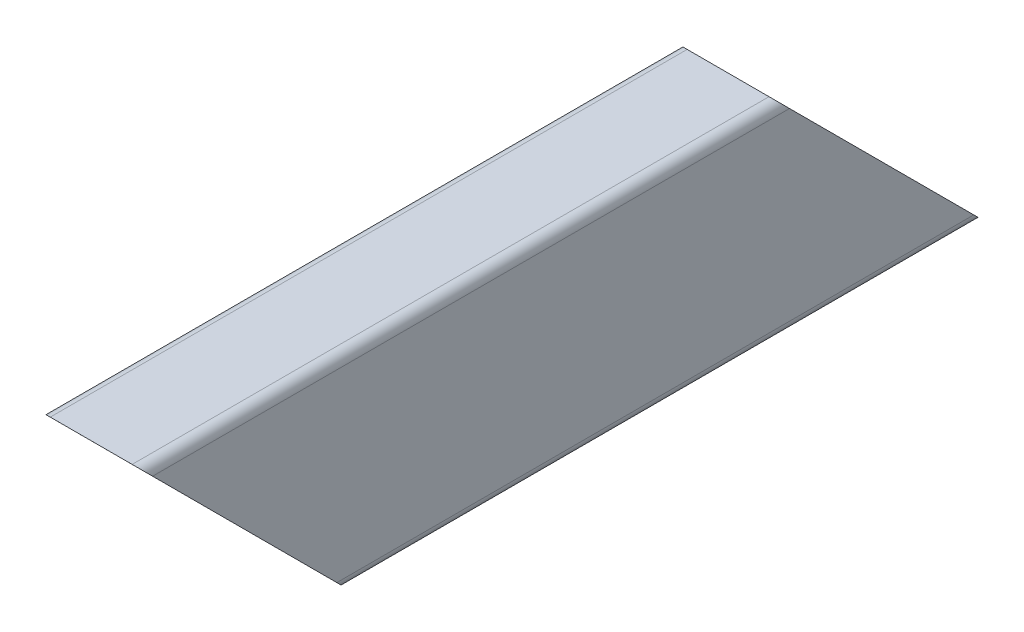
SolidWorks part; units mm, degrees
ref_plane "Спереди" through (0, 0, 0) normal (0, 0, 1) x (1, 0, 0)
ref_plane "Сверху" through (0, 0, 0) normal (0, 1, 0) x (1, 0, 0)
ref_plane "Справа" through (0, 0, 0) normal (1, 0, 0) x (0, 0, -1)
sketch "Эскиз1" plane through (0, 0, 0) normal (0, 0, 1) x (1, 0, 0)
  line L16 (-10, 50) -> (10, 50)
  line L17 (12.5, 47.5) -> (12.5, 2.5)
  line L18 (10, 0) -> (-10, 0)
  line L19 (-12.5, 2.5) -> (-12.5, 47.5)
  line L20 (-7.5, 47.5) -> (7.5, 47.5)
  line L21 (10, 45) -> (10, 5)
  line L22 (7.5, 2.5) -> (-7.5, 2.5)
  line L23 (-10, 5) -> (-10, 45)
  arc A16 (12.5, 47.5) -> (10, 50) centre (10, 47.5) ccw
  arc A17 (10, 0) -> (12.5, 2.5) centre (10, 2.5) ccw
  arc A18 (-12.5, 2.5) -> (-10, 0) centre (-10, 2.5) ccw
  arc A19 (-10, 50) -> (-12.5, 47.5) centre (-10, 47.5) ccw
  arc A20 (10, 45) -> (7.5, 47.5) centre (7.5, 45) ccw
  arc A21 (7.5, 2.5) -> (10, 5) centre (7.5, 5) ccw
  arc A22 (-10, 5) -> (-7.5, 2.5) centre (-7.5, 5) ccw
  arc A23 (-7.5, 47.5) -> (-10, 45) centre (-7.5, 45) ccw
extrude "Бобышка-Вытянуть1" add sketch "Эскиз1" against normal blind 205.56
sketch "Эскиз2" plane through (-12.5, 0, 0) normal (-1, 0, 0) x (0, 0, 1)
  line L0 (-205.56, 50) -> (-155.56, 50)
  line L1 (-155.56, 50) -> (-205.56, 0)
  line L2 (-205.56, 0) -> (-205.56, 50)
  line L3 (0.0035, 0) -> (-49.9965, 0)
  line L4 (-49.9965, 0) -> (0.0035, 50)
  line L5 (0.0035, 50) -> (0.0035, 0)
extrude "Вырез-Вытянуть1" cut sketch "Эскиз2" against normal blind 50
